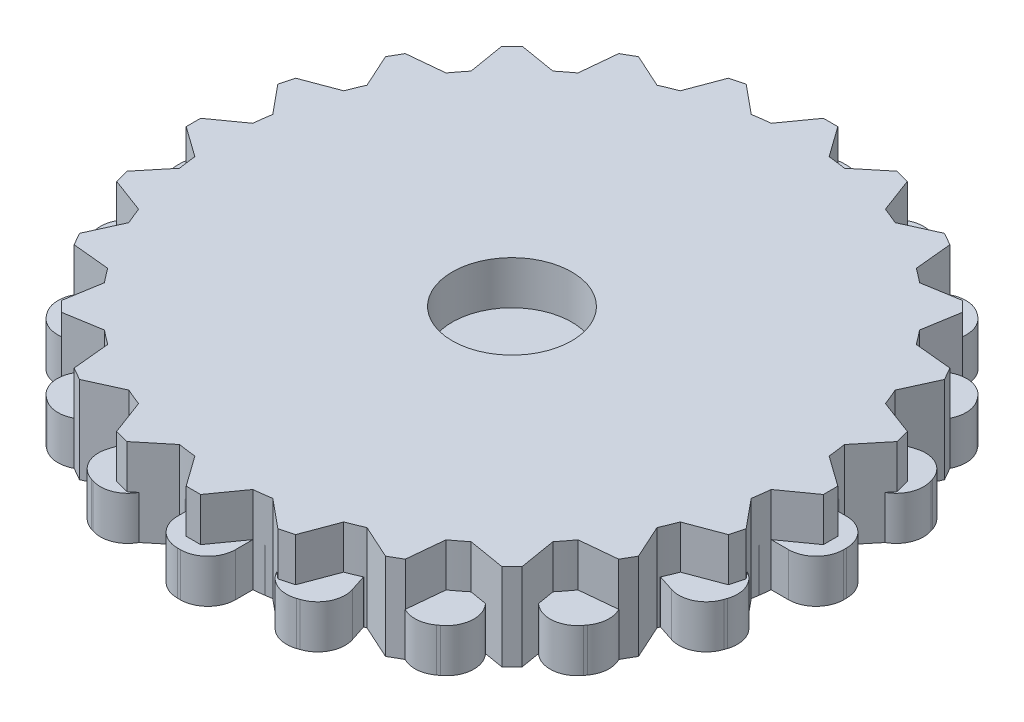
SolidWorks part; units mm, degrees
ref_plane "Front Plane" through (0, 0, 0) normal (0, 0, 1) x (1, 0, 0)
ref_plane "Top Plane" through (0, 0, 0) normal (0, 1, 0) x (1, 0, 0)
ref_plane "Right Plane" through (0, 0, 0) normal (1, 0, 0) x (0, 0, -1)
sketch "Sketch1" plane through (0, 0, 0) normal (0, 1, 0) x (1, 0, 0)
  line L111 (-0.5, 14.7462) -> (0.5, 14.7462)
  line L112 (0.5, 14.7462) -> (2, 12.5441)
  line L113 (-0.5, 14.7462) -> (-2, 12.5441)
  line L114 (6.433, 12.8885) -> (6.631, 10.2315)
  line L115 (5.567, 13.3885) -> (6.433, 12.8885)
  line L116 (5.567, 13.3885) -> (3.1669, 12.2315)
  line L117 (10.6423, 8.3132) -> (9.4853, 5.9131)
  line L118 (10.1423, 9.1792) -> (10.6423, 8.3132)
  line L119 (10.1423, 9.1792) -> (7.4853, 9.3772)
  line L120 (12, 2.2462) -> (9.798, 0.7462)
  line L121 (12, 3.2462) -> (12, 2.2462)
  line L122 (12, 3.2462) -> (9.798, 4.7462)
  line L123 (10.1423, -3.6868) -> (7.4853, -3.8849)
  line L124 (10.6423, -2.8208) -> (10.1423, -3.6868)
  line L125 (10.6423, -2.8208) -> (9.4853, -0.4208)
  line L126 (5.567, -7.8961) -> (3.1669, -6.7391)
  line L127 (6.433, -7.3961) -> (5.567, -7.8961)
  line L128 (6.433, -7.3961) -> (6.631, -4.7391)
  line L129 (-0.5, -9.2538) -> (-2, -7.0518)
  line L130 (0.5, -9.2538) -> (-0.5, -9.2538)
  line L131 (0.5, -9.2538) -> (2, -7.0518)
  line L132 (-6.433, -7.3961) -> (-6.631, -4.7391)
  line L133 (-5.567, -7.8961) -> (-6.433, -7.3961)
  line L134 (-5.567, -7.8961) -> (-3.1669, -6.7391)
  line L135 (-10.6423, -2.8208) -> (-9.4853, -0.4208)
  line L136 (-10.1423, -3.6868) -> (-10.6423, -2.8208)
  line L137 (-10.1423, -3.6868) -> (-7.4853, -3.8849)
  line L138 (-12, 3.2462) -> (-9.798, 4.7462)
  line L139 (-12, 2.2462) -> (-12, 3.2462)
  line L140 (-12, 2.2462) -> (-9.798, 0.7462)
  line L141 (-10.1423, 9.1792) -> (-7.4853, 9.3772)
  line L142 (-10.6423, 8.3132) -> (-10.1423, 9.1792)
  line L143 (-10.6423, 8.3132) -> (-9.4853, 5.9131)
  line L144 (-5.567, 13.3885) -> (-3.1669, 12.2315)
  line L145 (-6.433, 12.8885) -> (-5.567, 13.3885)
  line L146 (-6.433, 12.8885) -> (-6.631, 10.2315)
  arc A43 (-2, 12.5441) -> (-3.1669, 12.2315) centre (0, 2.7462) ccw
  arc A44 (-6.631, 10.2315) -> (-7.4853, 9.3772) centre (0, 2.7462) ccw
  arc A45 (-9.4853, 5.9131) -> (-9.798, 4.7462) centre (0, 2.7462) ccw
  arc A46 (-9.798, 0.7462) -> (-9.4853, -0.4208) centre (0, 2.7462) ccw
  arc A47 (-7.4853, -3.8849) -> (-6.631, -4.7391) centre (0, 2.7462) ccw
  arc A48 (-3.1669, -6.7391) -> (-2, -7.0518) centre (0, 2.7462) ccw
  arc A49 (2, -7.0518) -> (3.1669, -6.7391) centre (0, 2.7462) ccw
  arc A50 (6.631, -4.7391) -> (7.4853, -3.8849) centre (0, 2.7462) ccw
  arc A51 (9.4853, -0.4208) -> (9.798, 0.7462) centre (0, 2.7462) ccw
  arc A52 (9.798, 4.7462) -> (9.4853, 5.9131) centre (0, 2.7462) ccw
  arc A53 (7.4853, 9.3772) -> (6.631, 10.2315) centre (0, 2.7462) ccw
  arc A54 (3.1669, 12.2315) -> (2, 12.5441) centre (0, 2.7462) ccw
  point P6 (0, 0)
  point P8 (0, 0)
  point P9 (0, 0)
  point P12 (0, 2.7462)
  point P17 (0, 0)
  point P18 (0, 2.7462)
  point P22 (-2.5, 0.7462)
  point P63 (0, 0)
  point P68 (0, 0)
  point P69 (0, 2.7462)
  point P119 (0, 0)
  dimension "D1" = 20
  dimension "D8" = 12
sketch "Sketch2" plane through (0, 0, 0) normal (0, 1, 0) x (1, 0, 0)
  line L0 (-2, 0) -> (2, 0)
  line L1 (-23, -0.1) -> (-23, 0.1)
  line L2 (-21.1, 2) -> (-19.8997, 2)
  line L3 (-21.1, -2) -> (-19.8997, -2)
  line L4 (-20.6853, 4.6181) -> (-19.5438, 4.2472)
  line L5 (-19.4493, 8.4224) -> (-18.3078, 8.0515)
  line L6 (-21.9052, 7.0123) -> (-21.8434, 7.2025)
  line L7 (-18.2458, 10.7842) -> (-17.2748, 10.0787)
  line L8 (-15.8947, 14.0203) -> (-14.9237, 13.3148)
  line L9 (-18.6662, 13.4382) -> (-18.5486, 13.6)
  line L10 (-14.0203, 15.8947) -> (-13.3148, 14.9237)
  line L11 (-10.7842, 18.2458) -> (-10.0787, 17.2748)
  line L12 (-13.6, 18.5486) -> (-13.4382, 18.6662)
  line L13 (-8.4224, 19.4493) -> (-8.0515, 18.3078)
  line L14 (-4.6181, 20.6853) -> (-4.2472, 19.5438)
  line L15 (-7.2025, 21.8434) -> (-7.0123, 21.9052)
  line L16 (-2, 21.1) -> (-2, 19.8997)
  line L17 (2, 21.1) -> (2, 19.8997)
  line L18 (-0.1, 23) -> (0.1, 23)
  line L19 (4.6181, 20.6853) -> (4.2472, 19.5438)
  line L20 (8.4224, 19.4493) -> (8.0515, 18.3078)
  line L21 (7.0123, 21.9052) -> (7.2025, 21.8434)
  line L22 (10.7842, 18.2458) -> (10.0787, 17.2748)
  line L23 (14.0203, 15.8947) -> (13.3148, 14.9237)
  line L24 (13.4382, 18.6662) -> (13.6, 18.5486)
  line L25 (15.8947, 14.0203) -> (14.9237, 13.3148)
  line L26 (18.2458, 10.7842) -> (17.2748, 10.0787)
  line L27 (18.5486, 13.6) -> (18.6662, 13.4382)
  line L28 (19.4493, 8.4224) -> (18.3078, 8.0515)
  line L29 (20.6853, 4.6181) -> (19.5438, 4.2472)
  line L30 (21.8434, 7.2025) -> (21.9052, 7.0123)
  line L31 (21.1, 2) -> (19.8997, 2)
  line L32 (21.1, -2) -> (19.8997, -2)
  line L33 (23, 0.1) -> (23, -0.1)
  line L34 (20.6853, -4.6181) -> (19.5438, -4.2472)
  line L35 (19.4493, -8.4224) -> (18.3078, -8.0515)
  line L36 (21.9052, -7.0123) -> (21.8434, -7.2025)
  line L37 (18.2458, -10.7842) -> (17.2748, -10.0787)
  line L38 (15.8947, -14.0203) -> (14.9237, -13.3148)
  line L39 (18.6662, -13.4382) -> (18.5486, -13.6)
  line L40 (14.0203, -15.8947) -> (13.3148, -14.9237)
  line L41 (10.7842, -18.2458) -> (10.0787, -17.2748)
  line L42 (13.6, -18.5486) -> (13.4382, -18.6662)
  line L43 (8.4224, -19.4493) -> (8.0515, -18.3078)
  line L44 (4.6181, -20.6853) -> (4.2472, -19.5438)
  line L45 (7.2025, -21.8434) -> (7.0123, -21.9052)
  line L46 (2, -21.1) -> (2, -19.8997)
  line L47 (-2, -21.1) -> (-2, -19.8997)
  line L48 (0.1, -23) -> (-0.1, -23)
  line L49 (-4.6181, -20.6853) -> (-4.2472, -19.5438)
  line L50 (-8.4224, -19.4493) -> (-8.0515, -18.3078)
  line L51 (-7.0123, -21.9052) -> (-7.2025, -21.8434)
  line L52 (-10.7842, -18.2458) -> (-10.0787, -17.2748)
  line L53 (-14.0203, -15.8947) -> (-13.3148, -14.9237)
  line L54 (-13.4382, -18.6662) -> (-13.6, -18.5486)
  line L55 (-15.8947, -14.0203) -> (-14.9237, -13.3148)
  line L56 (-18.2458, -10.7842) -> (-17.2748, -10.0787)
  line L57 (-18.5486, -13.6) -> (-18.6662, -13.4382)
  line L58 (-19.4493, -8.4224) -> (-18.3078, -8.0515)
  line L59 (-20.6853, -4.6181) -> (-19.5438, -4.2472)
  line L60 (-21.8434, -7.2025) -> (-21.9052, -7.0123)
  arc A0 (-18.3078, -8.0515) -> (-17.2748, -10.0787) centre (0, 0) ccw
  arc A1 (-21.1, 2) -> (-23, 0.1) centre (-21.1, 0.1) ccw
  arc A2 (-21.1, -2) -> (-23, -0.1) centre (-21.1, -0.1) cw
  arc A3 (-20.6853, 4.6181) -> (-21.9052, 7.0123) centre (-20.0982, 6.4252) cw
  arc A4 (-19.4493, 8.4224) -> (-21.8434, 7.2025) centre (-20.0364, 6.6154) ccw
  arc A5 (-18.2458, 10.7842) -> (-18.6662, 13.4382) centre (-17.129, 12.3214) cw
  arc A6 (-15.8947, 14.0203) -> (-18.5486, 13.6) centre (-17.0115, 12.4832) ccw
  arc A7 (-14.0203, 15.8947) -> (-13.6, 18.5486) centre (-12.4832, 17.0115) cw
  arc A8 (-10.7842, 18.2458) -> (-13.4382, 18.6662) centre (-12.3214, 17.129) ccw
  arc A9 (-8.4224, 19.4493) -> (-7.2025, 21.8434) centre (-6.6154, 20.0364) cw
  arc A10 (-4.6181, 20.6853) -> (-7.0123, 21.9052) centre (-6.4252, 20.0982) ccw
  arc A11 (-2, 21.1) -> (-0.1, 23) centre (-0.1, 21.1) cw
  arc A12 (2, 21.1) -> (0.1, 23) centre (0.1, 21.1) ccw
  arc A13 (4.6181, 20.6853) -> (7.0123, 21.9052) centre (6.4252, 20.0982) cw
  arc A14 (8.4224, 19.4493) -> (7.2025, 21.8434) centre (6.6154, 20.0364) ccw
  arc A15 (10.7842, 18.2458) -> (13.4382, 18.6662) centre (12.3214, 17.129) cw
  arc A16 (14.0203, 15.8947) -> (13.6, 18.5486) centre (12.4832, 17.0115) ccw
  arc A17 (15.8947, 14.0203) -> (18.5486, 13.6) centre (17.0115, 12.4832) cw
  arc A18 (18.2458, 10.7842) -> (18.6662, 13.4382) centre (17.129, 12.3214) ccw
  arc A19 (19.4493, 8.4224) -> (21.8434, 7.2025) centre (20.0364, 6.6154) cw
  arc A20 (20.6853, 4.6181) -> (21.9052, 7.0123) centre (20.0982, 6.4252) ccw
  arc A21 (21.1, 2) -> (23, 0.1) centre (21.1, 0.1) cw
  arc A22 (21.1, -2) -> (23, -0.1) centre (21.1, -0.1) ccw
  arc A23 (20.6853, -4.6181) -> (21.9052, -7.0123) centre (20.0982, -6.4252) cw
  arc A24 (19.4493, -8.4224) -> (21.8434, -7.2025) centre (20.0364, -6.6154) ccw
  arc A25 (18.2458, -10.7842) -> (18.6662, -13.4382) centre (17.129, -12.3214) cw
  arc A26 (15.8947, -14.0203) -> (18.5486, -13.6) centre (17.0115, -12.4832) ccw
  arc A27 (14.0203, -15.8947) -> (13.6, -18.5486) centre (12.4832, -17.0115) cw
  arc A28 (10.7842, -18.2458) -> (13.4382, -18.6662) centre (12.3214, -17.129) ccw
  arc A29 (8.4224, -19.4493) -> (7.2025, -21.8434) centre (6.6154, -20.0364) cw
  arc A30 (4.6181, -20.6853) -> (7.0123, -21.9052) centre (6.4252, -20.0982) ccw
  arc A31 (2, -21.1) -> (0.1, -23) centre (0.1, -21.1) cw
  arc A32 (-2, -21.1) -> (-0.1, -23) centre (-0.1, -21.1) ccw
  arc A33 (-4.6181, -20.6853) -> (-7.0123, -21.9052) centre (-6.4252, -20.0982) cw
  arc A34 (-8.4224, -19.4493) -> (-7.2025, -21.8434) centre (-6.6154, -20.0364) ccw
  arc A35 (-10.7842, -18.2458) -> (-13.4382, -18.6662) centre (-12.3214, -17.129) cw
  arc A36 (-14.0203, -15.8947) -> (-13.6, -18.5486) centre (-12.4832, -17.0115) ccw
  arc A37 (-15.8947, -14.0203) -> (-18.5486, -13.6) centre (-17.0115, -12.4832) cw
  arc A38 (-18.2458, -10.7842) -> (-18.6662, -13.4382) centre (-17.129, -12.3214) ccw
  arc A39 (-19.4493, -8.4224) -> (-21.8434, -7.2025) centre (-20.0364, -6.6154) cw
  arc A40 (-20.6853, -4.6181) -> (-21.9052, -7.0123) centre (-20.0982, -6.4252) ccw
  arc A41 (-19.8997, -2) -> (-19.5438, -4.2472) centre (0, 0) ccw
  arc A42 (-19.5438, 4.2472) -> (-19.8997, 2) centre (0, 0) ccw
  arc A43 (-17.2748, 10.0787) -> (-18.3078, 8.0515) centre (0, 0) ccw
  arc A44 (-13.3148, 14.9237) -> (-14.9237, 13.3148) centre (0, 0) ccw
  arc A45 (-8.0515, 18.3078) -> (-10.0787, 17.2748) centre (0, 0) ccw
  arc A46 (-2, 19.8997) -> (-4.2472, 19.5438) centre (0, 0) ccw
  arc A47 (4.2472, 19.5438) -> (2, 19.8997) centre (0, 0) ccw
  arc A48 (10.0787, 17.2748) -> (8.0515, 18.3078) centre (0, 0) ccw
  arc A49 (14.9237, 13.3148) -> (13.3148, 14.9237) centre (0, 0) ccw
  arc A50 (18.3078, 8.0515) -> (17.2748, 10.0787) centre (0, 0) ccw
  arc A51 (19.8997, 2) -> (19.5438, 4.2472) centre (0, 0) ccw
  arc A52 (19.5438, -4.2472) -> (19.8997, -2) centre (0, 0) ccw
  arc A53 (17.2748, -10.0787) -> (18.3078, -8.0515) centre (0, 0) ccw
  arc A54 (13.3148, -14.9237) -> (14.9237, -13.3148) centre (0, 0) ccw
  arc A55 (8.0515, -18.3078) -> (10.0787, -17.2748) centre (0, 0) ccw
  arc A56 (2, -19.8997) -> (4.2472, -19.5438) centre (0, 0) ccw
  arc A57 (-10.0787, -17.2748) -> (-8.0515, -18.3078) centre (0, 0) ccw
  arc A58 (-4.2472, -19.5438) -> (-2, -19.8997) centre (0, 0) ccw
  arc A59 (-14.9237, -13.3148) -> (-13.3148, -14.9237) centre (0, 0) ccw
  point P6 (0, 0)
  point P10 (-23, 2)
  point P170 (0, 0)
  dimension "D1" = 40
  dimension "D4" = 1.9
  dimension "D5" = 20
extrude "Boss-Extrude3" add sketch "Sketch2" along normal blind 3
sketch "Sketch3" plane through (0, 0, 0) normal (0, 1, 0) x (1, 0, 0)
  line L0 (-22, 0) -> (22, 0)
  line L1 (22, -0.5) -> (22, 0.5)
  line L2 (22, 0.5) -> (19.8997, 2)
  line L3 (22, -0.5) -> (19.8997, -2)
  line L4 (21.3798, -5.2111) -> (19.7393, -3.2186)
  line L5 (21.121, -6.177) -> (21.3798, -5.2111)
  line L6 (21.121, -6.177) -> (18.704, -7.0823)
  line L7 (19.3026, -10.567) -> (18.2337, -8.2178)
  line L8 (18.8026, -11.433) -> (19.3026, -10.567)
  line L9 (18.8026, -11.433) -> (16.2337, -11.6819)
  line L10 (15.9099, -15.2028) -> (15.4855, -12.657)
  line L11 (15.2028, -15.9099) -> (15.9099, -15.2028)
  line L12 (15.2028, -15.9099) -> (12.657, -15.4855)
  line L13 (11.433, -18.8026) -> (11.6819, -16.2337)
  line L14 (10.567, -19.3026) -> (11.433, -18.8026)
  line L15 (10.567, -19.3026) -> (8.2178, -18.2337)
  line L16 (6.177, -21.121) -> (7.0823, -18.704)
  line L17 (5.2111, -21.3798) -> (6.177, -21.121)
  line L18 (5.2111, -21.3798) -> (3.2186, -19.7393)
  line L19 (0.5, -22) -> (2, -19.8997)
  line L20 (-0.5, -22) -> (0.5, -22)
  line L21 (-0.5, -22) -> (-2, -19.8997)
  line L22 (-5.2111, -21.3798) -> (-3.2186, -19.7393)
  line L23 (-6.177, -21.121) -> (-5.2111, -21.3798)
  line L24 (-6.177, -21.121) -> (-7.0823, -18.704)
  line L25 (-10.567, -19.3026) -> (-8.2178, -18.2337)
  line L26 (-11.433, -18.8026) -> (-10.567, -19.3026)
  line L27 (-11.433, -18.8026) -> (-11.6819, -16.2337)
  line L28 (-15.2028, -15.9099) -> (-12.657, -15.4855)
  line L29 (-15.9099, -15.2028) -> (-15.2028, -15.9099)
  line L30 (-15.9099, -15.2028) -> (-15.4855, -12.657)
  line L31 (-18.8026, -11.433) -> (-16.2337, -11.6819)
  line L32 (-19.3026, -10.567) -> (-18.8026, -11.433)
  line L33 (-19.3026, -10.567) -> (-18.2337, -8.2178)
  line L34 (-21.121, -6.177) -> (-18.704, -7.0823)
  line L35 (-21.3798, -5.2111) -> (-21.121, -6.177)
  line L36 (-21.3798, -5.2111) -> (-19.7393, -3.2186)
  line L37 (-22, -0.5) -> (-19.8997, -2)
  line L38 (-22, 0.5) -> (-22, -0.5)
  line L39 (-22, 0.5) -> (-19.8997, 2)
  line L40 (-21.3798, 5.2111) -> (-19.7393, 3.2186)
  line L41 (-21.121, 6.177) -> (-21.3798, 5.2111)
  line L42 (-21.121, 6.177) -> (-18.704, 7.0823)
  line L43 (-19.3026, 10.567) -> (-18.2337, 8.2178)
  line L44 (-18.8026, 11.433) -> (-19.3026, 10.567)
  line L45 (-18.8026, 11.433) -> (-16.2337, 11.6819)
  line L46 (-15.9099, 15.2028) -> (-15.4855, 12.657)
  line L47 (-15.2028, 15.9099) -> (-15.9099, 15.2028)
  line L48 (-15.2028, 15.9099) -> (-12.657, 15.4855)
  line L49 (-11.433, 18.8026) -> (-11.6819, 16.2337)
  line L50 (-10.567, 19.3026) -> (-11.433, 18.8026)
  line L51 (-10.567, 19.3026) -> (-8.2178, 18.2337)
  line L52 (-6.177, 21.121) -> (-7.0823, 18.704)
  line L53 (-5.2111, 21.3798) -> (-6.177, 21.121)
  line L54 (-5.2111, 21.3798) -> (-3.2186, 19.7393)
  line L55 (-0.5, 22) -> (-2, 19.8997)
  line L56 (0.5, 22) -> (-0.5, 22)
  line L57 (0.5, 22) -> (2, 19.8997)
  line L58 (5.2111, 21.3798) -> (3.2186, 19.7393)
  line L59 (6.177, 21.121) -> (5.2111, 21.3798)
  line L60 (6.177, 21.121) -> (7.0823, 18.704)
  line L61 (10.567, 19.3026) -> (8.2178, 18.2337)
  line L62 (11.433, 18.8026) -> (10.567, 19.3026)
  line L63 (11.433, 18.8026) -> (11.6819, 16.2337)
  line L64 (15.2028, 15.9099) -> (12.657, 15.4855)
  line L65 (15.9099, 15.2028) -> (15.2028, 15.9099)
  line L66 (15.9099, 15.2028) -> (15.4855, 12.657)
  line L67 (18.8026, 11.433) -> (16.2337, 11.6819)
  line L68 (19.3026, 10.567) -> (18.8026, 11.433)
  line L69 (19.3026, 10.567) -> (18.2337, 8.2178)
  line L70 (21.121, 6.177) -> (18.704, 7.0823)
  line L71 (21.3798, 5.2111) -> (21.121, 6.177)
  line L72 (21.3798, 5.2111) -> (19.7393, 3.2186)
  arc A0 (-8.2178, -18.2337) -> (-7.0823, -18.704) centre (0, 0) ccw
  arc A1 (-12.657, -15.4855) -> (-11.6819, -16.2337) centre (0, 0) ccw
  arc A2 (-16.2337, -11.6819) -> (-15.4855, -12.657) centre (0, 0) ccw
  arc A3 (-18.704, -7.0823) -> (-18.2337, -8.2178) centre (0, 0) ccw
  arc A4 (-19.8997, -2) -> (-19.7393, -3.2186) centre (0, 0) ccw
  arc A5 (-19.7393, 3.2186) -> (-19.8997, 2) centre (0, 0) ccw
  arc A6 (-18.2337, 8.2178) -> (-18.704, 7.0823) centre (0, 0) ccw
  arc A7 (-15.4855, 12.657) -> (-16.2337, 11.6819) centre (0, 0) ccw
  arc A8 (-11.6819, 16.2337) -> (-12.657, 15.4855) centre (0, 0) ccw
  arc A9 (-7.0823, 18.704) -> (-8.2178, 18.2337) centre (0, 0) ccw
  arc A10 (-2, 19.8997) -> (-3.2186, 19.7393) centre (0, 0) ccw
  arc A11 (3.2186, 19.7393) -> (2, 19.8997) centre (0, 0) ccw
  arc A12 (8.2178, 18.2337) -> (7.0823, 18.704) centre (0, 0) ccw
  arc A13 (12.657, 15.4855) -> (11.6819, 16.2337) centre (0, 0) ccw
  arc A14 (16.2337, 11.6819) -> (15.4855, 12.657) centre (0, 0) ccw
  arc A15 (18.704, 7.0823) -> (18.2337, 8.2178) centre (0, 0) ccw
  arc A16 (19.8997, 2) -> (19.7393, 3.2186) centre (0, 0) ccw
  arc A17 (19.7393, -3.2186) -> (19.8997, -2) centre (0, 0) ccw
  arc A18 (18.2337, -8.2178) -> (18.704, -7.0823) centre (0, 0) ccw
  arc A19 (-3.2186, -19.7393) -> (-2, -19.8997) centre (0, 0) ccw
  arc A20 (2, -19.8997) -> (3.2186, -19.7393) centre (0, 0) ccw
  arc A21 (7.0823, -18.704) -> (8.2178, -18.2337) centre (0, 0) ccw
  arc A22 (11.6819, -16.2337) -> (12.657, -15.4855) centre (0, 0) ccw
  arc A23 (15.4855, -12.657) -> (16.2337, -11.6819) centre (0, 0) ccw
  point P6 (0, 0)
  point P7 (0, -12.952)
  point P8 (-6.2727, 0)
  point P9 (11.4668, 0)
  point P10 (0, 0)
  point P108 (0, 0)
  dimension "D1" = 40
  dimension "D2" = 22
  dimension "D3" = 2
  dimension "D4" = 24
extrude "Boss-Extrude5" add sketch "Sketch3" along normal blind 6 separate body contours L2 A16 L72 L71 L70 A15 L69 L68 L67 A14 L66 L65 L64 A13 L63 L62 L61 A12 L60 L59 L58 A11 L57 L56 L55 A10 L54 L53 L52 A9 L51 L50 L49 A8 L48 L47 L46 A7 L45 L44 L43 A6 L42 L41 L40 A5 L39 L38 L0 L1 | L10 A23 L9 L8 L7 A18 L6 L5 L4 A17 L3 L1 L0 L38 L37 A4 L36 L35 L34 A3 L33 L32 L31 A2 L30 L29 L28 A1 L27 L26 L25 A0 L24 L23 L22 A19 L21 L20 L19 A20 L18 L17 L16 A21 L15 L14 L13 A22 L12 L11
extrude "Boss-Extrude6" add sketch "Sketch1" along normal blind 3 separate body
sketch "Sketch4" plane through (0, 6, 0) normal (0, 1, 0) x (1, 0, 0)
  circle A0 centre (0, 0) radius 4.125
  dimension "D1" = 8.25
extrude "Cut-Extrude1" cut sketch "Sketch4" against normal blind 10
